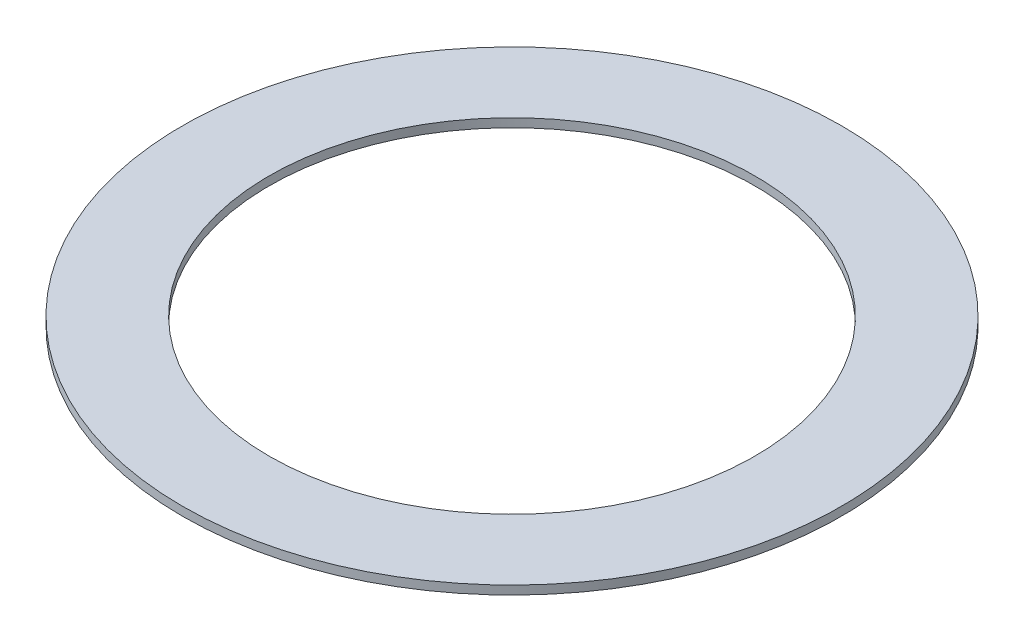
SolidWorks part; units mm, degrees
ref_plane "Front Plane" through (0, 0, 0) normal (0, 0, 1) x (1, 0, 0)
ref_plane "Top Plane" through (0, 0, 0) normal (0, 1, 0) x (1, 0, 0)
ref_plane "Right Plane" through (0, 0, 0) normal (1, 0, 0) x (0, 0, -1)
sketch "Sketch1" plane through (0, 0, 0) normal (0, 1, 0) x (1, 0, 0)
  circle A0 centre (0, 0) radius 88.9
  circle A1 centre (0, 0) radius 120.65
  dimension "D1" = 177.8
  dimension "D2" = 241.3
extrude "Boss-Extrude1" add sketch "Sketch1" along normal blind 3.175
equation "\"2x3.5\"=3.60815"
